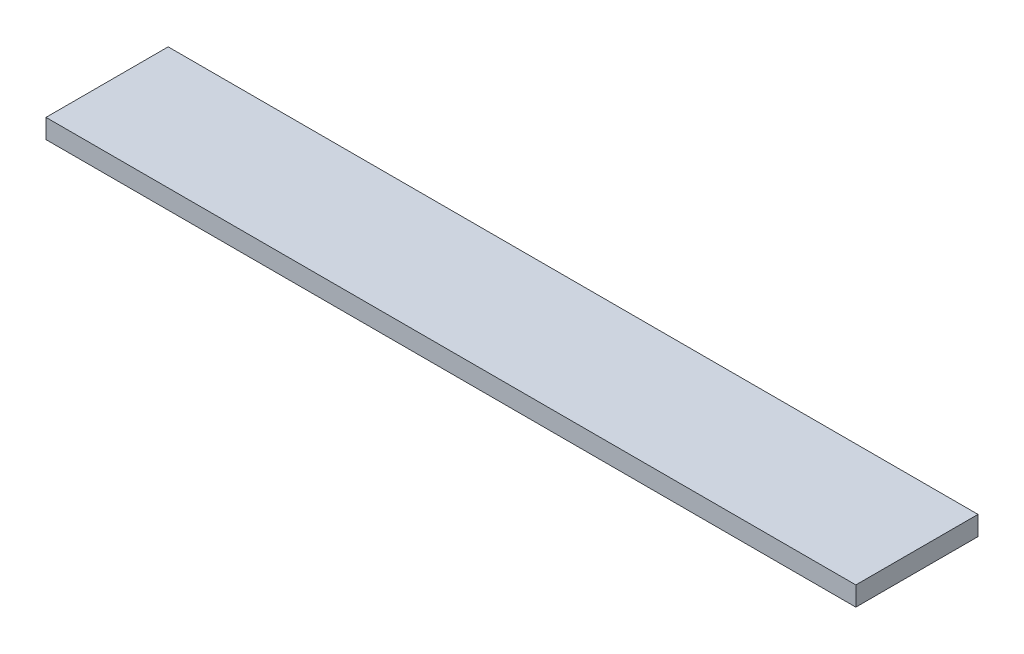
SolidWorks part; units mm, degrees
material "Oak"
ref_plane "Front Plane" through (0, 0, 0) normal (0, 0, 1) x (1, 0, 0)
ref_plane "Top Plane" through (0, 0, 0) normal (0, 1, 0) x (1, 0, 0)
ref_plane "Right Plane" through (0, 0, 0) normal (1, 0, 0) x (0, 0, -1)
sketch "Sketch1" plane through (0, 0, 0) normal (0, 1, 0) x (1, 0, 0)
  line L1 (0, 0) -> (800.1, 0)
  line L2 (0, 0) -> (0, 120.7008)
  line L3 (0, 120.7008) -> (800.1, 120.7008)
  line L4 (800.1, 0) -> (800.1, 120.7008)
  dimension "D1" = 120.7008
  dimension "D2" = 800.1
extrude "Boss-Extrude1" add sketch "Sketch1" along normal blind 19.05
